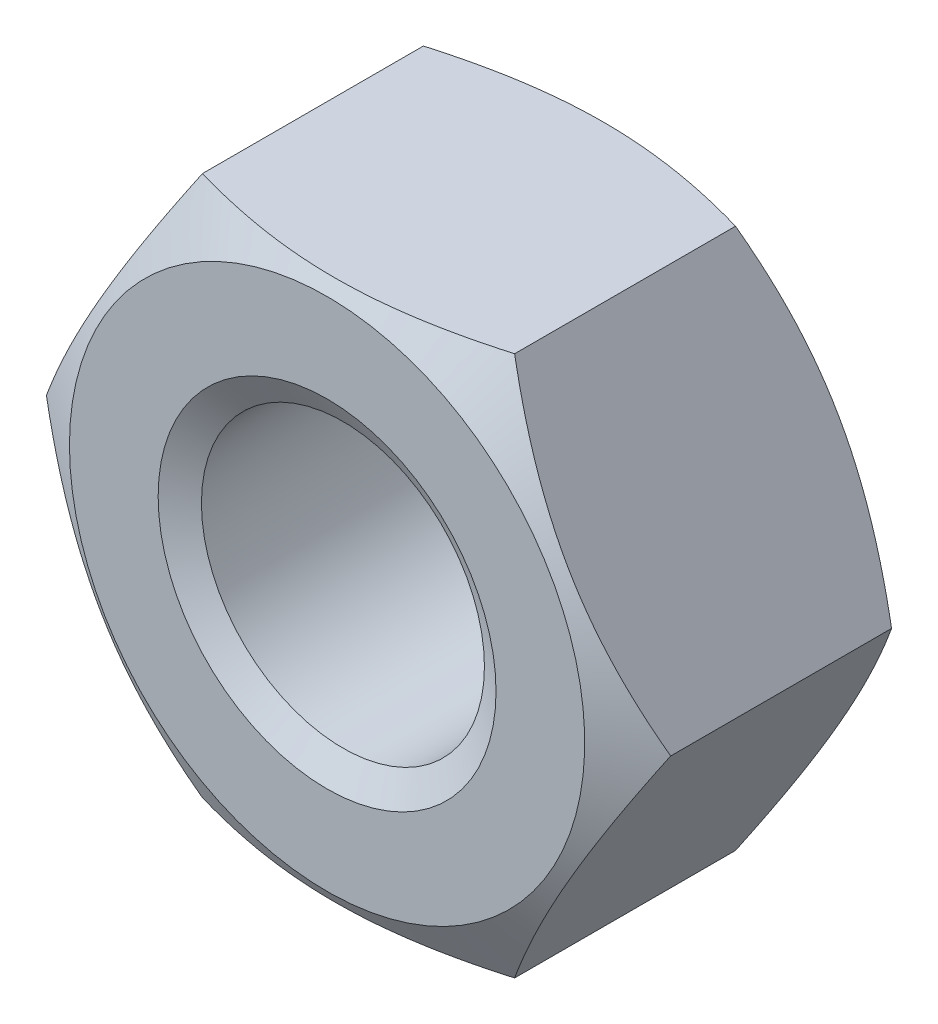
SolidWorks part; units mm, degrees
ref_plane "Front" through (0, 0, 0) normal (0, 0, 1) x (1, 0, 0)
ref_plane "Top" through (0, 0, 0) normal (0, 1, 0) x (1, 0, 0)
ref_plane "Right" through (0, 0, 0) normal (1, 0, 0) x (0, 0, -1)
sketch "Sketch1" plane through (0, 0, 0) normal (0, 0, 1) x (1, 0, 0)
  line L1 (9.2376, 0) -> (4.6188, 8)
  line L2 (4.6188, 8) -> (-4.6188, 8)
  line L3 (-4.6188, 8) -> (-9.2376, 0)
  line L4 (-9.2376, 0) -> (-4.6188, -8)
  line L5 (-4.6188, -8) -> (4.6188, -8)
  line L6 (4.6188, -8) -> (9.2376, 0)
  circle A0 centre (0, 0) radius 8 construction
  circle A1 centre (0, 0) radius 4.188
  dimension "D" = 8.376
  dimension "s" = 16
extrude "BaseNut" add sketch "Sketch1" against normal blind 8.4
cosmetic thread "ThreadCosmetic1" [suppressed] parameters "D"=10
sketch "Sketch2" plane through (0, 0, 0) normal (0, 1, 0) x (1, 0, 0)
  line L0 (-9.2376, 8.4) -> (-7.625, 8.4)
  line L2 (-7.625, 8.4) -> (-9.2376, 7.469)
  line L3 (-9.2376, 7.469) -> (-9.2376, 8.4)
  line L4 (0, 3.3759) -> (0, -9.8171) construction
  line L6 (-9.7712, 4.2) -> (9.8853, 4.2) construction
  line L7 (-9.2376, 0.931) -> (-9.2376, 0)
  line L8 (-7.625, 0) -> (-9.2376, 0.931)
  line L9 (-9.2376, 0) -> (-7.625, 0)
  dimension "D1" = 30
  dimension "dw" = 15.25
  dimension "D2" = 4.2
revolve "Double-Chamfer" cut sketch "Sketch2" angle 360 about L4
chamfer "EndChamfer" distance 0.812 angle 30 2 edges at (4.188, 0, -8.4) (4.188, 0, 0)
sketch "Sketch3" plane through (0, 0, 0) normal (0, 1, 0) x (1, 0, 0)
  line L0 (-4.8912, 7.588) -> (-4.188, 7.182)
  line L1 (-4.188, 7.182) -> (-3.376, 7.182)
  line L2 (-3.376, 7.182) -> (-3.376, 7.994)
  line L3 (-3.376, 7.994) -> (-4.188, 7.994)
  line L4 (-4.188, 7.994) -> (-4.8912, 7.588)
  line L5 (0, 7.4383) -> (0, 16.8806) construction
  dimension "D1" = 0.812
  dimension "D2" = 8.376
revolve "Cut-Revolve10" [suppressed] cut sketch "Sketch3" angle 360 about L5
pattern_linear "LPattern10" [suppressed] count 9 spacing 0.9744 along (0, 0, -1)
equation "\"dw@Sketch2\" = \"s@Sketch1\"-0.75"
equation "\"D2@Sketch2\" = \"m@BaseNut\" / 2"
equation "\"D2@Sketch3\" = \"D@Sketch1\""
equation "\"D1@Sketch3\" =  (\"D@ThreadCosmetic1\"   - \"D@Sketch1\")  / 2"
equation "\"D3@LPattern10\" = \"D1@Sketch3\" * 1.2"
equation "\"D1@LPattern10\" = \"m@BaseNut\"/\"D3@LPattern10\""
